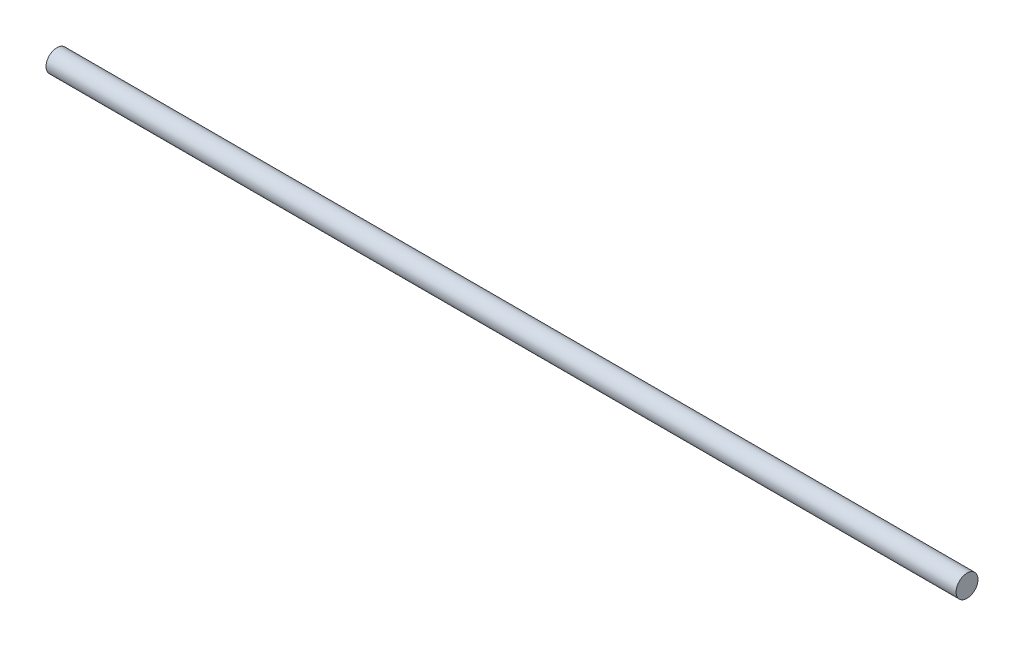
SolidWorks part; units mm, degrees
ref_plane "Front Plane" through (0, 0, 0) normal (0, 0, 1) x (1, 0, 0)
ref_plane "Top Plane" through (0, 0, 0) normal (0, 1, 0) x (1, 0, 0)
ref_plane "Right Plane" through (0, 0, 0) normal (1, 0, 0) x (0, 0, -1)
sketch "Sketch1" plane through (0, 0, 0) normal (0, 0, 1) x (1, 0, 0)
  line L0 (-124.5, 0) -> (124.5, 0)
  line L1 (0, 3) -> (0, 0)
  line L4 (124.5, 3) -> (0, 3)
  line L6 (-124.5, 3) -> (-124.5, 0)
  line L7 (-124.5, 3) -> (0, 3)
  line L9 (124.5, 3) -> (124.5, 0)
  point P3 (0, 0)
  dimension "D2" = 249
  dimension "D1" = 3
revolve "Revolve2" add sketch "Sketch1" angle 360 about L0
